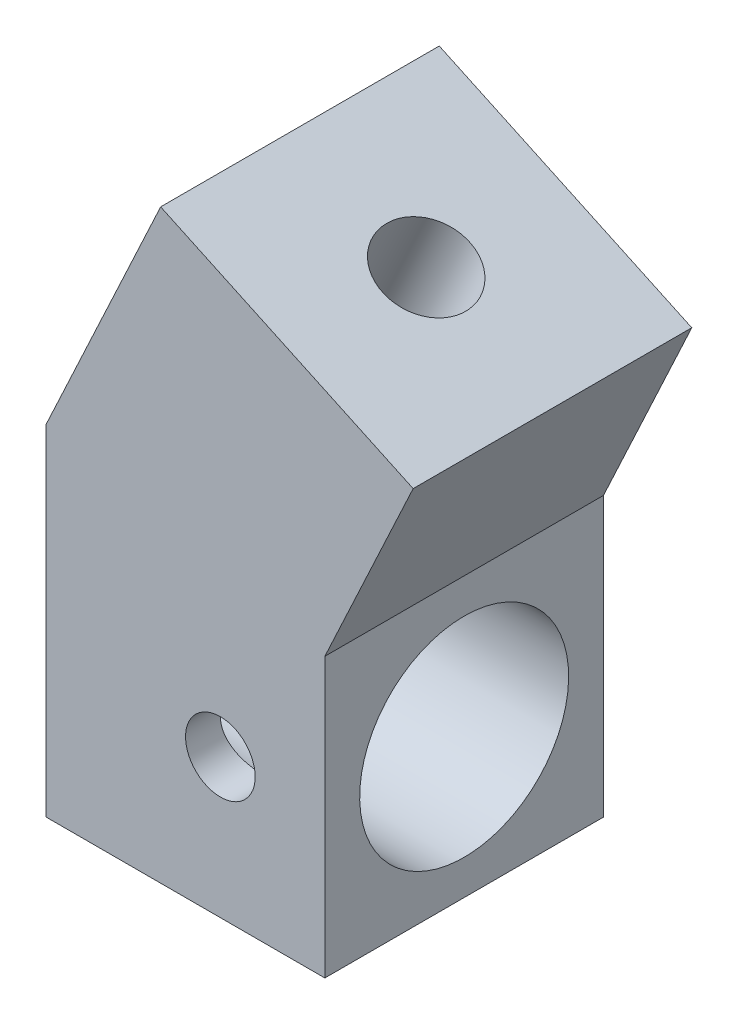
SolidWorks part; units mm, degrees
ref_plane "Front Plane" through (0, 0, 0) normal (0, 0, 1) x (1, 0, 0)
ref_plane "Top Plane" through (0, 0, 0) normal (0, 1, 0) x (1, 0, 0)
ref_plane "Right Plane" through (0, 0, 0) normal (1, 0, 0) x (0, 0, -1)
sketch "Sketch2" plane through (0, 0, 0) normal (0, 0, 1) x (1, 0, 0)
  line L0 (0, 0) -> (0, 9.7736)
  line L1 (0, 9.7736) -> (3.2852, 16.8188)
  line L2 (3.2852, 16.8188) -> (10.5357, 13.4378)
  line L3 (10.5357, 13.4378) -> (8, 8)
  line L4 (8, 8) -> (8, 0)
  line L5 (8, 0) -> (0, 0)
  point P10 (0, 9.0064)
  dimension "D1" = 8
  dimension "D2" = 155
  dimension "D4" = 8
  dimension "D5" = 6
extrude "Boss-Extrude1" add sketch "Sketch2" along normal blind 8 contours L5 L4 L3 L2 L1 L0
sketch "Sketch3" plane through (8, 0, 0) normal (1, 0, 0) x (0, 0, -1)
  line L1 (-8, 0) -> (0, 0) construction
  line L2 (0, 8) -> (0, 0) construction
  circle A0 centre (-4, 4) radius 3
  point P2 (0, 0)
  dimension "D2" = 4
  dimension "D3" = 6
  dimension "D1" = 4
extrude "Cut-Extrude1" cut sketch "Sketch3" against normal up to next
sketch "Sketch4" plane through (0, 0, 8) normal (0, 0, 1) x (1, 0, 0)
  line L0 (8, 0) -> (0, 0) construction
  line L1 (8, 8) -> (8, 0) construction
  circle A0 centre (5, 4) radius 1
  dimension "D1" = 2
  dimension "D2" = 4
  dimension "D3" = 3
extrude "Cut-Extrude2" cut sketch "Sketch4" against normal up to next
sketch "Sketch5" plane through (7.0287, 15.0732, 0) normal (0.4226, 0.9063, 0) x (0.9063, -0.4226, 0)
  line L0 (-4.1305, 0) -> (3.8695, 0) construction
  line L1 (-4.1305, -8) -> (-4.1305, 0) construction
  circle A0 centre (-0.1305, -4) radius 1.25
  dimension "D1" = 2.5
  dimension "D2" = 4
  dimension "D3" = 4
extrude "Cut-Extrude3" cut sketch "Sketch5" against normal blind 3
